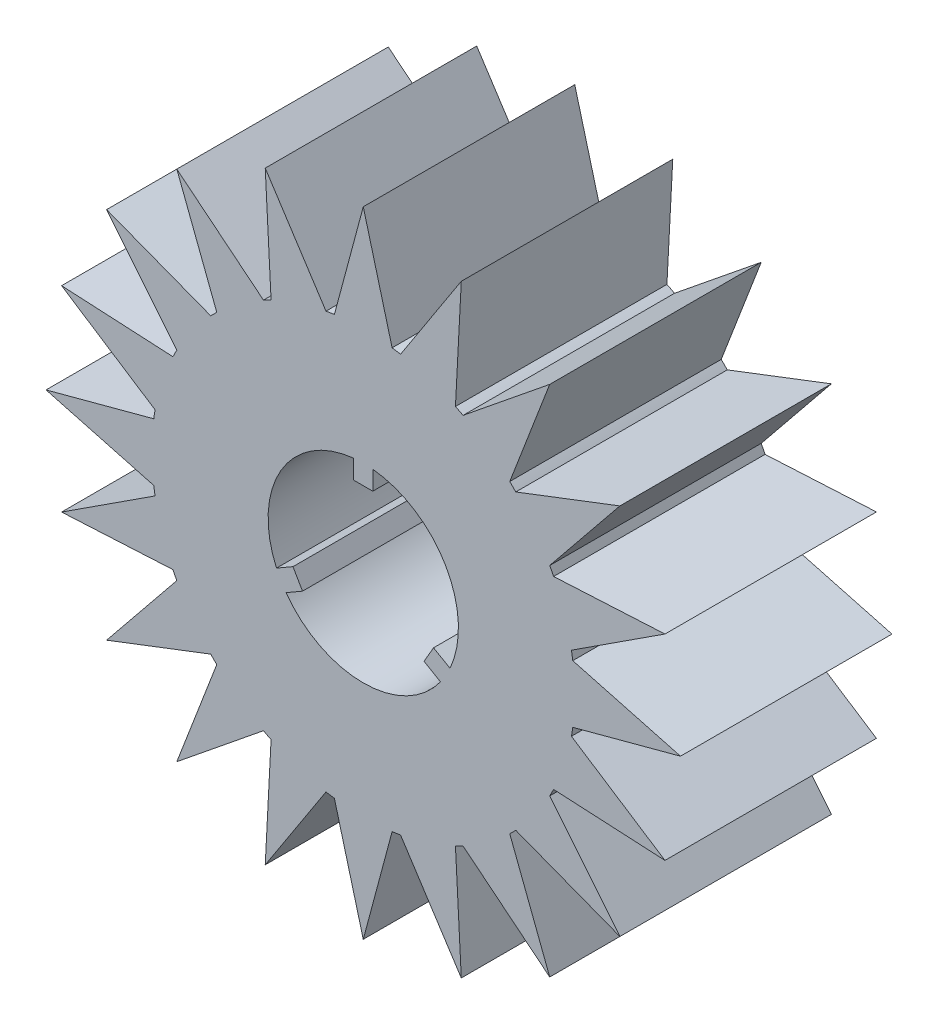
SolidWorks part; units mm, degrees
ref_plane "Front Plane" through (0, 0, 0) normal (0, 0, 1) x (1, 0, 0)
ref_plane "Top Plane" through (0, 0, 0) normal (0, 1, 0) x (1, 0, 0)
ref_plane "Right Plane" through (0, 0, 0) normal (1, 0, 0) x (0, 0, -1)
sketch "Sketch1" plane through (0, 0, 0) normal (0, 0, 1) x (1, 0, 0)
  line L0 (0, 15) -> (-1.3648, 9.9064)
  line L1 (0, 15) -> (1.3648, 9.9064)
  line L2 (4.6353, 14.2658) -> (4.3593, 8.9998)
  line L3 (4.6353, 14.2658) -> (1.7632, 9.8433)
  line L4 (8.8168, 12.1353) -> (6.927, 7.2122)
  line L5 (8.8168, 12.1353) -> (4.7187, 8.8167)
  line L6 (12.1353, 8.8168) -> (8.8167, 4.7187)
  line L7 (12.1353, 8.8168) -> (7.2122, 6.927)
  line L8 (14.2658, 4.6353) -> (9.8433, 1.7632)
  line L9 (14.2658, 4.6353) -> (8.9998, 4.3593)
  line L10 (15, 0) -> (9.9064, -1.3648)
  line L11 (15, 0) -> (9.9064, 1.3648)
  line L12 (14.2658, -4.6353) -> (8.9998, -4.3593)
  line L13 (14.2658, -4.6353) -> (9.8433, -1.7632)
  line L14 (12.1353, -8.8168) -> (7.2122, -6.927)
  line L15 (12.1353, -8.8168) -> (8.8167, -4.7187)
  line L16 (8.8168, -12.1353) -> (4.7187, -8.8167)
  line L17 (8.8168, -12.1353) -> (6.927, -7.2122)
  line L18 (4.6353, -14.2658) -> (1.7632, -9.8433)
  line L19 (4.6353, -14.2658) -> (4.3593, -8.9998)
  line L20 (0, -15) -> (-1.3648, -9.9064)
  line L21 (0, -15) -> (1.3648, -9.9064)
  line L22 (-4.6353, -14.2658) -> (-4.3593, -8.9998)
  line L23 (-4.6353, -14.2658) -> (-1.7632, -9.8433)
  line L24 (-8.8168, -12.1353) -> (-6.927, -7.2122)
  line L25 (-8.8168, -12.1353) -> (-4.7187, -8.8167)
  line L26 (-12.1353, -8.8168) -> (-8.8167, -4.7187)
  line L27 (-12.1353, -8.8168) -> (-7.2122, -6.927)
  line L28 (-14.2658, -4.6353) -> (-9.8433, -1.7632)
  line L29 (-14.2658, -4.6353) -> (-8.9998, -4.3593)
  line L30 (-15, 0) -> (-9.9064, 1.3648)
  line L31 (-15, 0) -> (-9.9064, -1.3648)
  line L32 (-14.2658, 4.6353) -> (-8.9998, 4.3593)
  line L33 (-14.2658, 4.6353) -> (-9.8433, 1.7632)
  line L34 (-12.1353, 8.8168) -> (-7.2122, 6.927)
  line L35 (-12.1353, 8.8168) -> (-8.8167, 4.7187)
  line L36 (-8.8168, 12.1353) -> (-4.7187, 8.8167)
  line L37 (-8.8168, 12.1353) -> (-6.927, 7.2122)
  line L38 (-4.6353, 14.2658) -> (-1.7632, 9.8433)
  line L39 (-4.6353, 14.2658) -> (-4.3593, 8.9998)
  line L40 (0.45, 3.5774) -> (-0.45, 3.5774)
  line L41 (-0.45, 3.5774) -> (-0.45, 4.4774)
  line L42 (0.45, 3.5774) -> (0.45, 4.4774)
  line L43 (2.8732, -2.1784) -> (3.6526, -2.6284)
  line L44 (2.8732, -2.1784) -> (3.3232, -1.399)
  line L45 (3.3232, -1.399) -> (4.1026, -1.849)
  line L46 (-3.3232, -1.399) -> (-4.1026, -1.849)
  line L47 (-3.3232, -1.399) -> (-2.8732, -2.1784)
  line L48 (-2.8732, -2.1784) -> (-3.6526, -2.6284)
  arc A0 (-1.7632, -9.8433) -> (-1.3648, -9.9064) centre (0, 0) ccw
  arc A1 (-0.45, 4.4774) -> (-4.1026, -1.849) centre (0, 0) ccw
  arc A4 (-4.7187, -8.8167) -> (-4.3593, -8.9998) centre (0, 0) ccw
  arc A5 (-7.2122, -6.927) -> (-6.927, -7.2122) centre (0, 0) ccw
  arc A6 (-8.9998, -4.3593) -> (-8.8167, -4.7187) centre (0, 0) ccw
  arc A7 (-9.9064, -1.3648) -> (-9.8433, -1.7632) centre (0, 0) ccw
  arc A8 (-9.8433, 1.7632) -> (-9.9064, 1.3648) centre (0, 0) ccw
  arc A9 (-8.8167, 4.7187) -> (-8.9998, 4.3593) centre (0, 0) ccw
  arc A10 (-6.927, 7.2122) -> (-7.2122, 6.927) centre (0, 0) ccw
  arc A11 (-4.3593, 8.9998) -> (-4.7187, 8.8167) centre (0, 0) ccw
  arc A12 (-1.3648, 9.9064) -> (-1.7632, 9.8433) centre (0, 0) ccw
  arc A13 (1.7632, 9.8433) -> (1.3648, 9.9064) centre (0, 0) ccw
  arc A14 (4.7187, 8.8167) -> (4.3593, 8.9998) centre (0, 0) ccw
  arc A15 (7.2122, 6.927) -> (6.927, 7.2122) centre (0, 0) ccw
  arc A16 (8.9998, 4.3593) -> (8.8167, 4.7187) centre (0, 0) ccw
  arc A17 (9.9064, 1.3648) -> (9.8433, 1.7632) centre (0, 0) ccw
  arc A18 (9.8433, -1.7632) -> (9.9064, -1.3648) centre (0, 0) ccw
  arc A19 (8.8167, -4.7187) -> (8.9998, -4.3593) centre (0, 0) ccw
  arc A20 (6.927, -7.2122) -> (7.2122, -6.927) centre (0, 0) ccw
  arc A21 (4.3593, -8.9998) -> (4.7187, -8.8167) centre (0, 0) ccw
  arc A22 (1.3648, -9.9064) -> (1.7632, -9.8433) centre (0, 0) ccw
  arc A26 (4.1026, -1.849) -> (0.45, 4.4774) centre (0, 0) ccw
  arc A27 (-3.6526, -2.6284) -> (3.6526, -2.6284) centre (0, 0) ccw
  point P9 (0, 3.5774)
  point P69 (0, 0)
  point P81 (0, 0)
  dimension "D2" = 20
  dimension "D3" = 9
  dimension "D4" = 30
  dimension "D1" = 30
  dimension "D6" = 0.9
  dimension "D7" = 0.9
  dimension "D5" = 20
  dimension "D8" = 3
extrude "Boss-Extrude1" add sketch "Sketch1" along normal blind 10 contours L21 A22 L18 L19 A21 L16 L17 A20 L14 L15 A19 L12 L13 A18 L10 L11 A17 L8 L9 A16 L6 L7 A15 L4 L5 A14 L2 L3 A13 L1 L0 A12 L38 L39 A11 L36 L37 A10 L34 L35 A9 L32 L33 A8 L30 L31 A7 L28 L29 A6 L26
equation "\"Outer Tooth Diameter\" = 30mm"
equation "\"Outer Body Diameter\"= \"Outer Tooth Diameter\" - 10mm"
equation "\"Inner Body Diameter\"= 9mm"
equation "\"Slot Extrude Length\"= 0.9mm"
equation "\"D2@Sketch1\"=\"Outer Body Diameter\""
equation "\"D3@Sketch1\"=\"Inner Body Diameter\""
equation "\"D1@Sketch1\"=\"Outer Tooth Diameter\""
equation "\"D6@Sketch1\"=\"Slot Extrude Length\""
equation "\"Slot Extrude Width\"= 0.9mm"
equation "\"D7@Sketch1\"=\"Slot Extrude Width\""
equation "\"Gear Thickness\"= 10mm"
equation "\"D1@Boss-Extrude1\"=\"Gear Thickness\""
